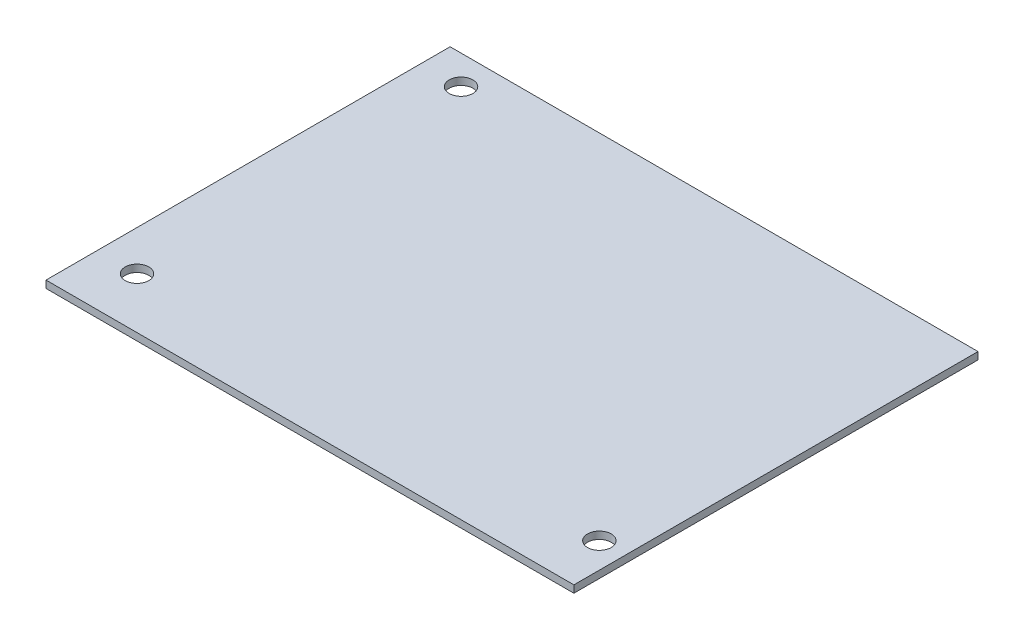
SolidWorks part; units mm, degrees
ref_plane "Front Plane" through (0, 0, 0) normal (0, 0, 1) x (1, 0, 0)
ref_plane "Top Plane" through (0, 0, 0) normal (0, 1, 0) x (1, 0, 0)
ref_plane "Right Plane" through (0, 0, 0) normal (1, 0, 0) x (0, 0, -1)
sketch "Sketch1" plane through (0, 0, 0) normal (0, 1, 0) x (1, 0, 0)
  line L1 (0, 0) -> (-145, 0)
  line L2 (0, 0) -> (0, 111)
  line L3 (0, 111) -> (-145, 111)
  line L4 (-145, 0) -> (-145, 111)
  circle A0 centre (-134, 14) radius 3.25
  circle A1 centre (-7, 14) radius 3.25
  circle A3 centre (-134, 103) radius 3.25
  dimension "D3" = 6.5
  dimension "D6" = 6.5
  dimension "D7" = 7
  dimension "D8" = 14
  dimension "D9" = 6.5
  dimension "D10" = 11
  dimension "D11" = 8
  dimension "D1" = 145
  dimension "D2" = 111
  dimension "D4" = 11
  dimension "D5" = 14
extrude "Boss-Extrude1" add sketch "Sketch1" along normal blind 2
